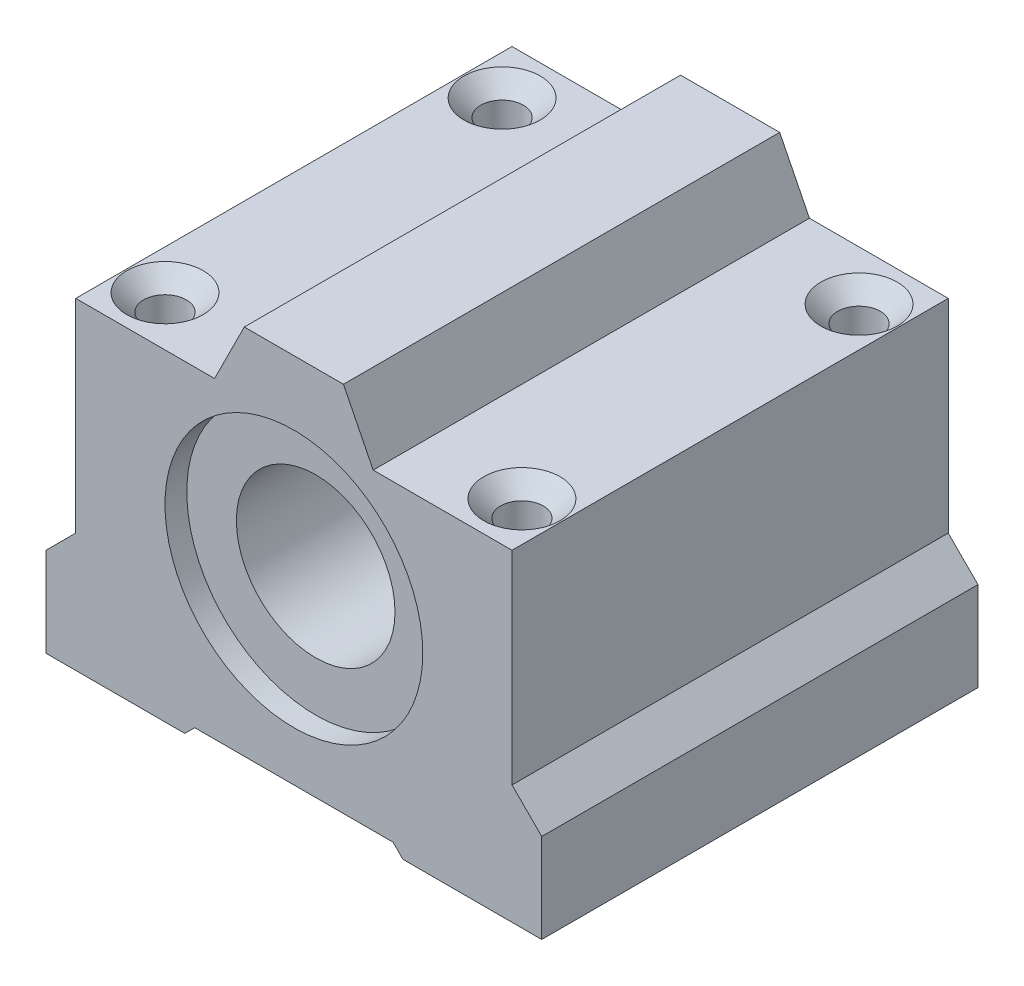
SolidWorks part; units mm, degrees
material "Liga 6061"
ref_plane "Plano frontal" through (0, 0, 0) normal (0, 0, 1) x (1, 0, 0)
ref_plane "Plano superior" through (0, 0, 0) normal (0, 1, 0) x (1, 0, 0)
ref_plane "Plano direito" through (0, 0, 0) normal (1, 0, 0) x (0, 0, -1)
sketch "Esboço1" plane through (0, 0, 0) normal (0, 0, 1) x (1, 0, 0)
  line L0 (-22, 13.5) -> (-22, -7)
  line L1 (-22, -7) -> (-25, -10)
  line L2 (-25, -10) -> (-25, -19)
  line L3 (-25, -19) -> (-11, -19)
  line L4 (-11, -19) -> (-10, -18)
  line L5 (-10, -18) -> (10, -18)
  line L6 (10, -18) -> (11, -19)
  line L7 (11, -19) -> (25, -19)
  line L8 (25, -19) -> (25, -10)
  line L9 (25, -10) -> (22, -7)
  line L10 (22, -7) -> (22, 13.5)
  line L11 (22, 13.5) -> (8, 13.5)
  line L12 (-5, 19.5) -> (-8, 13.5)
  line L13 (5, 19.5) -> (-5, 19.5)
  line L14 (8, 13.5) -> (5, 19.5)
  line L15 (-8, 13.5) -> (-22, 13.5)
  circle A0 centre (0, 0) radius 8
  dimension "D1" = 16
  dimension "D2" = 50
  dimension "D3" = 14
  dimension "D4" = 14
  dimension "D5" = 1
  dimension "D6" = 1
  dimension "D7" = 1
  dimension "D8" = 32.5
  dimension "D9" = 9
  dimension "D10" = 12
  dimension "D11" = 44
  dimension "D13" = 25
  dimension "D14" = 3
  dimension "D15" = 19
  dimension "D16" = 3
  dimension "D17" = 14
  dimension "D18" = 10
  dimension "D19" = 38.5
extrude "Extrusão1" add sketch "Esboço1" along normal blind 44
sketch "Esboço2" plane through (0, 0, 44) normal (0, 0, 1) x (1, 0, 0)
  circle A0 centre (0, 0) radius 13
  dimension "D1" = 26
extrude "Extrusão2" cut sketch "Esboço2" against normal blind 2.2
sketch "Esboço3" plane through (0, 0, 0) normal (0, 0, -1) x (-1, 0, 0)
  circle A0 centre (0, 0) radius 13
  dimension "D1" = 26
extrude "Extrusão3" cut sketch "Esboço3" against normal blind 2.2
sketch "Esboço4" plane through (0, 13.5, 0) normal (0, 1, 0) x (1, 0, 0)
  line L3 (-25, -44) -> (-25, 0) construction
  line L4 (25, -44) -> (25, 0) construction
  line L5 (22, 0) -> (8, 0) construction
  circle A0 centre (18, -5) radius 2.15
  circle A1 centre (18, -39) radius 2.15
  circle A2 centre (-18, -5) radius 2.15
  circle A3 centre (-18, -39) radius 2.15
  dimension "D5" = 4.3
  dimension "D1" = 7
  dimension "D2" = 7
  dimension "D3" = 34
  dimension "D4" = 5
extrude "Extrusão4" cut sketch "Esboço4" against normal through all
hole_wizard "Escareado para parafuso de máquina com cabeça chata de M52" positions "3DSketch1" profile "Esboço6" countersink size "M5" standard "Métrico Ansi"
sketch3d "3DSketch1"
  line L0 (-18, -19, 39) -> (-18, 13.5, 39) construction
  line L1 (-18, -19, 5) -> (-18, 13.5, 5) construction
  line L2 (18, -19, 5) -> (18, 13.5, 5) construction
  line L3 (18, -19, 39) -> (18, 13.5, 39) construction
  point P0 (-18, -19, 39)
  point P4 (-18, -19, 5)
  point P8 (18, -19, 5)
  point P12 (18, -19, 39)
sketch "Esboço6" plane through (-18, -19, 39) normal (1, 0, 0) x (0, 0, -1)
  line L0 (0, 0) -> (0, 13.6524)
  line L1 (0, 13.6524) -> (2.75, 12)
  line L2 (2.75, 12) -> (2.75, 1.75)
  line L3 (2.75, 1.75) -> (4.5, 0)
  line L5 (4.5, 0) -> (0, 0)
  line L6 (-2.75, 1.75) -> (-4.5, 0) construction
  line L10 (0, 13.6524) -> (-2.75, 12) construction
  line L11 (0, -6.35) -> (0, 107.95) construction
  dimension "Hole Dia." = 5.5
  dimension "Hole Depth" = 12
  dimension "Near C'Sink Dia." = 9
  dimension "Near C'Sink Angle" = 90
  dimension "Drill Angle" = 118
chamfer "Chanfro1" distance 1.7 angle 45 4 edges at (15.85, 13.5, 5) (15.85, 13.5, 39) (-20.15, 13.5, 39) (-20.15, 13.5, 5)
